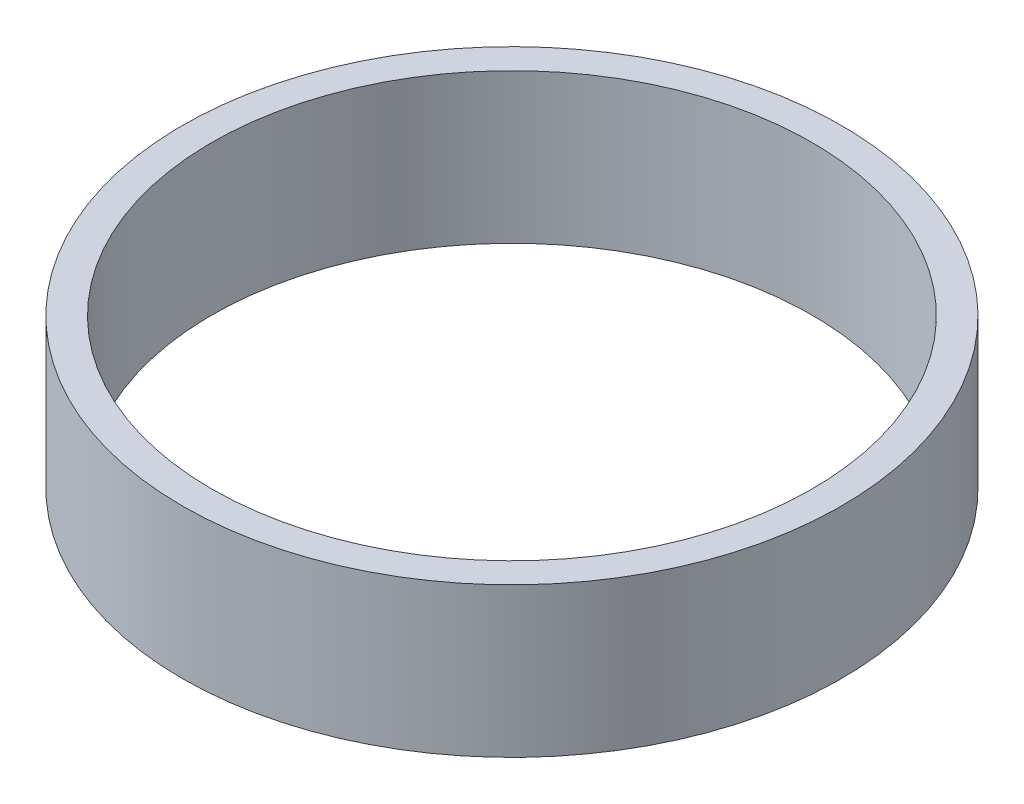
SolidWorks part; units mm, degrees
ref_plane "前视基准面" through (0, 0, 0) normal (0, 0, 1) x (1, 0, 0)
ref_plane "上视基准面" through (0, 0, 0) normal (0, 1, 0) x (1, 0, 0)
ref_plane "右视基准面" through (0, 0, 0) normal (1, 0, 0) x (0, 0, -1)
sketch "草图1" plane through (0, 0, 0) normal (0, 0, 1) x (1, 0, 0)
  line L0 (0, 161.3762) -> (0, 0) construction
  line L1 (141.7365, 0) -> (-131.7984, 0) construction
  line L2 (28, 0) -> (28, 12.7)
  line L3 (25.5, 12.7) -> (28, 12.7)
  line L4 (25.5, 0) -> (28, 0)
  line L7 (25.5, 12.7) -> (25.5, 0)
  dimension "D2" = 28
  dimension "D3" = 12.7
  dimension "D11" = 25.5
revolve "旋转1" add sketch "草图1" angle 360 about L0
cosmetic thread "装饰螺纹线1" parameters "D2"=52
